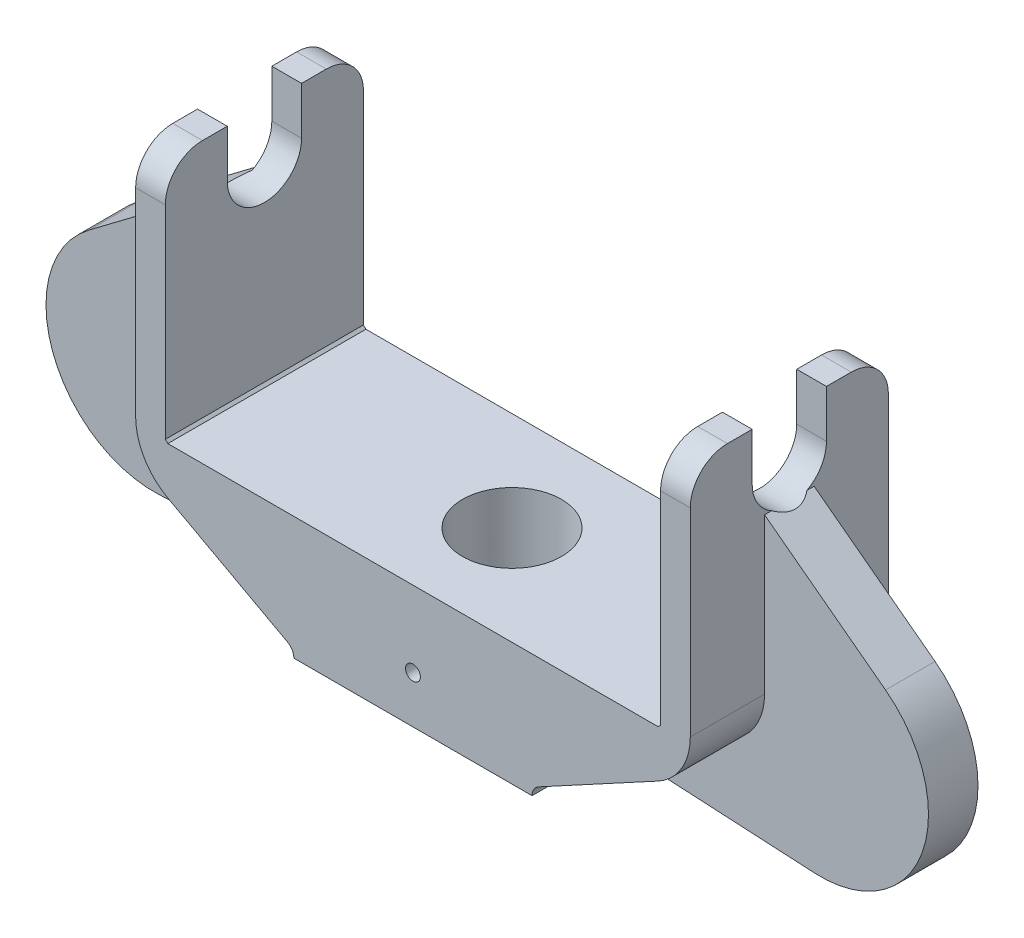
SolidWorks part; units mm, degrees
material "Plain Carbon Steel"
ref_plane "Front Plane" through (0, 0, 0) normal (0, 0, 1) x (1, 0, 0)
ref_plane "Top Plane" through (0, 0, 0) normal (0, 1, 0) x (1, 0, 0)
ref_plane "Right Plane" through (0, 0, 0) normal (1, 0, 0) x (0, 0, -1)
sketch "Sketch1" plane through (0, 0, 0) normal (0, 0, 1) x (1, 0, 0)
  line L0 (0, -0.4211) -> (0, 1.53) construction
  line L1 (-2.405, -0.95) -> (2.405, -0.95)
  line L2 (-5, 6.43) -> (-5, 1.58)
  line L3 (-4.95, 1.53) -> (4.95, 1.53)
  line L4 (5, 1.58) -> (5, 6.43)
  line L5 (-5, 6.43) -> (-5.6, 6.43)
  line L6 (-5.6, 6.43) -> (-5.6, 1.6744)
  line L7 (5, 6.43) -> (5.6, 6.43)
  line L8 (5.6, 6.43) -> (5.6, 1.6744)
  line L9 (-4.9455, 0.5754) -> (-2.5359, -0.7302)
  line L10 (2.5359, -0.7302) -> (4.9455, 0.5754)
  line L11 (-5, 1.58) -> (-4.95, 1.53)
  line L12 (4.95, 1.53) -> (5, 1.58)
  circle A0 centre (0, 0) radius 0.15
  arc A1 (-2.405, -0.95) -> (-2.5359, -0.7302) centre (-2.655, -0.95) ccw
  arc A2 (2.405, -0.95) -> (2.5359, -0.7302) centre (2.655, -0.95) cw
  arc A3 (-5.6, 1.6744) -> (-4.9455, 0.5754) centre (-4.35, 1.6744) ccw
  arc A4 (5.6, 1.6744) -> (4.9455, 0.5754) centre (4.35, 1.6744) cw
  point P12 (-5, 1.53)
  point P14 (5, 1.53)
  point P23 (-5.6, 0.93)
  point P26 (5.6, 0.93)
  dimension "D1" = 0.3
  dimension "D4" = 0.25
  dimension "D10" = 1.25
  dimension "D2" = 4.81
  dimension "D3" = 0.95
  dimension "D5" = 10
  dimension "D6" = 2.48
  dimension "D7" = 0.6
  dimension "D8" = 7.38
  dimension "D9" = 0.6
  dimension "D11" = 0.05
  dimension "D12" = 45
  dimension "D13" = 0.05
  dimension "D14" = 45
extrude "Boss-Extrude1" add sketch "Sketch1" along normal mid plane 4
sketch "Sketch2" plane through (0, 0, 0) normal (0, 0, 1) x (1, 0, 0)
  line L0 (2.5359, -0.7302) -> (4.9455, 0.5754) construction
  line L1 (5.6, 1.6744) -> (5.6, 6.43) construction
  line L2 (2.5359, -0.7302) -> (4.9455, 0.5754)
  line L3 (5.6, 1.6744) -> (5.6, 4.81)
  line L4 (5.6, 4.81) -> (8.0429, 2.9672)
  line L5 (6.6127, -0.95) -> (2.5359, -0.7302)
  line L6 (5.6, 6.43) -> (5, 6.43) construction
  line L7 (0, -1.5961) -> (0, 3.439) construction
  line L11 (-2.5359, -0.7302) -> (-4.9455, 0.5754)
  line L12 (-6.6127, -0.95) -> (-2.5359, -0.7302)
  line L13 (-5.6, 4.81) -> (-8.0429, 2.9672)
  line L14 (-5.6, 1.6744) -> (-5.6, 4.81)
  arc A0 (4.9455, 0.5754) -> (5.6, 1.6744) centre (4.35, 1.6744) ccw construction
  arc A1 (4.9455, 0.5754) -> (5.6, 1.6744) centre (4.35, 1.6744) ccw
  arc A2 (8.0429, 2.9672) -> (6.6127, -0.95) centre (6.73, 1.2268) cw
  arc A4 (-4.9455, 0.5754) -> (-5.6, 1.6744) centre (-4.35, 1.6744) cw
  arc A5 (-8.0429, 2.9672) -> (-6.6127, -0.95) centre (-6.73, 1.2268) ccw
  dimension "D1" = 1.62
  dimension "D3" = 2.18
  dimension "D2" = 3.06
extrude "Boss-Extrude3" add sketch "Sketch2" along normal mid plane 1
sketch "Sketch4" plane through (0, 0, 0) normal (1, 0, 0) x (0, 0, -1)
  line L0 (-2, -0.95) -> (2, -0.95) construction
  line L1 (0.75, 5.47) -> (0.75, 6.97)
  line L2 (0.75, 6.97) -> (-0.75, 6.97)
  line L3 (-0.75, 6.97) -> (-0.75, 5.47)
  arc A0 (-0.75, 5.47) -> (0.75, 5.47) centre (0, 5.47) ccw
  dimension "D1" = 6.42
  dimension "D2" = 0.75
  dimension "D3" = 1.5
extrude "Cut-Extrude1" cut sketch "Sketch4" against normal through all both and the other way through all
sketch "Sketch5" plane through (5.6, 0, 0) normal (1, 0, 0) x (0, 0, -1)
  line L0 (2, 1.6744) -> (2, 6.43) construction
  line L1 (0.75, 6.43) -> (2, 6.43) construction
  line L2 (2, 6.43) -> (2, 5.68)
  line L3 (2, 6.43) -> (1.25, 6.43)
  line L4 (-2, 1.6744) -> (-2, 6.43) construction
  line L5 (-2, 6.43) -> (-0.75, 6.43) construction
  line L6 (-2, 6.43) -> (-2, 5.68)
  line L7 (-1.25, 6.43) -> (-2, 6.43)
  arc A0 (-2, 5.68) -> (-1.25, 6.43) centre (-1.25, 5.68) cw
  arc A1 (2, 5.68) -> (1.25, 6.43) centre (1.25, 5.68) ccw
  dimension "D1" = 0.75
extrude "Cut-Extrude2" cut sketch "Sketch5" against normal through all both
sketch "Sketch6" plane through (0, 0, 0) normal (0, 1, 0) x (1, 0, 0)
  circle A0 centre (0, 0) radius 1
  dimension "D1" = 2
extrude "Cut-Extrude3" cut sketch "Sketch6" along normal through all both and the other way through all
